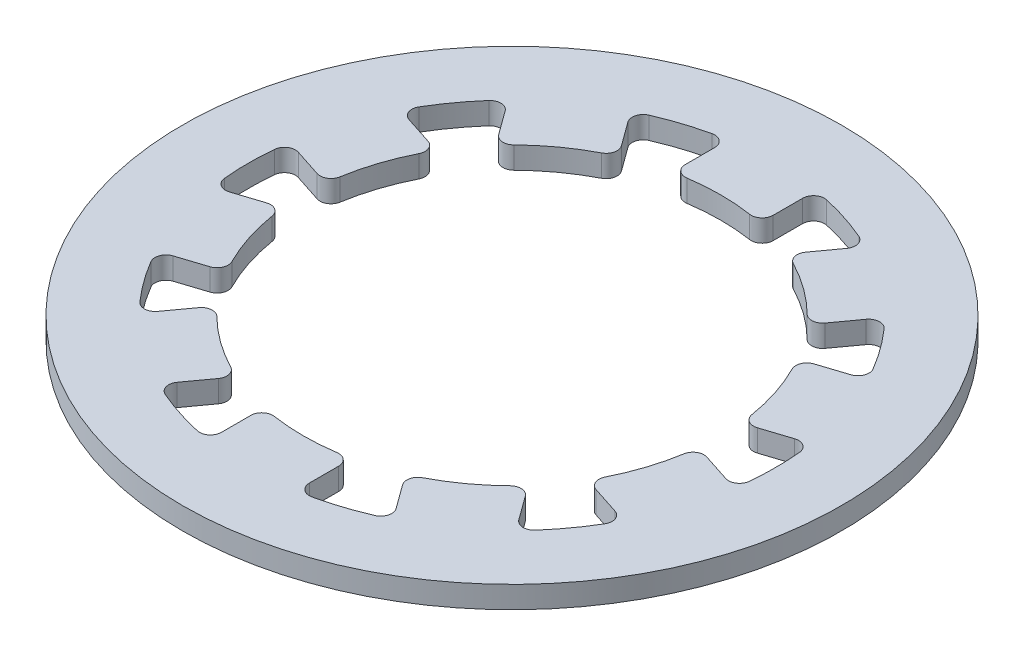
SolidWorks part; units mm, degrees
ref_plane "Front Plane" through (0, 0, 0) normal (0, 0, 1) x (1, 0, 0)
ref_plane "Top Plane" through (0, 0, 0) normal (0, 1, 0) x (1, 0, 0)
ref_plane "Right Plane" through (0, 0, 0) normal (1, 0, 0) x (0, 0, -1)
sketch "Sketch1" plane through (0, 0, 0) normal (0, 1, 0) x (1, 0, 0)
  line L0 (0, 18.9947) -> (0, -20.503) construction
  line L1 (-18.0992, 0) -> (25.0749, 0) construction
  line L2 (-2, 11.225) -> (-2, 9.8869)
  line L3 (2, 11.225) -> (2, 9.8869)
  line L4 (2, 18.9947) -> (2, -20.503) construction
  line L5 (-2, 18.9947) -> (-2, -20.503) construction
  line L6 (8.2159, 7.9056) -> (7.4294, 6.8231)
  line L7 (4.9798, 10.2568) -> (4.1933, 9.1742)
  line L8 (11.2936, 1.5666) -> (10.021, 1.1531)
  line L9 (10.0575, 5.3708) -> (8.7849, 4.9573)
  line L10 (10.0575, -5.3708) -> (8.7849, -4.9573)
  line L11 (11.2936, -1.5666) -> (10.021, -1.1531)
  line L12 (4.9798, -10.2568) -> (4.1933, -9.1742)
  line L13 (8.2159, -7.9056) -> (7.4294, -6.8231)
  line L14 (-2, -11.225) -> (-2, -9.8869)
  line L15 (2, -11.225) -> (2, -9.8869)
  line L16 (-8.2159, -7.9056) -> (-7.4294, -6.8231)
  line L17 (-4.9798, -10.2568) -> (-4.1933, -9.1742)
  line L18 (-11.2936, -1.5666) -> (-10.021, -1.1531)
  line L19 (-10.0575, -5.3708) -> (-8.7849, -4.9573)
  line L20 (-10.0575, 5.3708) -> (-8.7849, 4.9573)
  line L21 (-11.2936, 1.5666) -> (-10.021, 1.1531)
  line L22 (-4.9798, 10.2568) -> (-4.1933, 9.1742)
  line L23 (-8.2159, 7.9056) -> (-7.4294, 6.8231)
  circle A0 centre (0, 0) radius 15
  arc A1 (-4.3679, 8.4363) -> (-6.6736, 6.7611) centre (0, 0) ccw
  arc A2 (-8.9952, 7.9427) -> (-10.3336, 6.1005) centre (0, 0) ccw
  arc A3 (-8.4925, 4.2577) -> (-9.3732, 1.5472) centre (0, 0) ccw
  arc A4 (-9.3732, -1.5472) -> (-8.4925, -4.2577) centre (0, 0) ccw
  arc A5 (-6.6736, -6.7611) -> (-4.3679, -8.4363) centre (0, 0) ccw
  arc A6 (-1.425, -9.3925) -> (1.425, -9.3925) centre (0, 0) ccw
  arc A7 (4.3679, -8.4363) -> (6.6736, -6.7611) centre (0, 0) ccw
  arc A8 (8.4925, -4.2577) -> (9.3732, -1.5472) centre (0, 0) ccw
  arc A9 (9.3732, 1.5472) -> (8.4925, 4.2577) centre (0, 0) ccw
  arc A10 (6.6736, 6.7611) -> (4.3679, 8.4363) centre (0, 0) ccw
  arc A11 (1.425, 9.3925) -> (-1.425, 9.3925) centre (0, 0) ccw
  arc A12 (-11.9459, 1.1385) -> (-11.9459, -1.1385) centre (0, 0) ccw
  arc A13 (-10.3336, -6.1005) -> (-8.9952, -7.9427) centre (0, 0) ccw
  arc A14 (-4.7743, -11.0094) -> (-2.6087, -11.713) centre (0, 0) ccw
  arc A15 (2.6087, -11.713) -> (4.7743, -11.0094) centre (0, 0) ccw
  arc A16 (8.9952, -7.9427) -> (10.3336, -6.1005) centre (0, 0) ccw
  arc A17 (11.9459, -1.1385) -> (11.9459, 1.1385) centre (0, 0) ccw
  arc A18 (10.3336, 6.1005) -> (8.9952, 7.9427) centre (0, 0) ccw
  arc A19 (-2.6087, 11.713) -> (-4.7743, 11.0094) centre (0, 0) ccw
  arc A20 (4.7743, 11.0094) -> (2.6087, 11.713) centre (0, 0) ccw
  arc A21 (-11.2936, 1.5666) -> (-11.9459, 1.1385) centre (-11.4481, 1.0911) ccw
  arc A22 (-11.2936, -1.5666) -> (-11.9459, -1.1385) centre (-11.4481, -1.0911) cw
  arc A23 (-10.021, -1.1531) -> (-9.3732, -1.5472) centre (-9.8665, -1.6286) cw
  arc A24 (-8.7849, -4.9573) -> (-8.4925, -4.2577) centre (-8.9394, -4.4818) ccw
  arc A25 (-10.0575, -5.3708) -> (-10.3336, -6.1005) centre (-9.903, -5.8463) ccw
  arc A26 (-8.2159, -7.9056) -> (-8.9952, -7.9427) centre (-8.6204, -7.6117) cw
  arc A27 (-7.4294, -6.8231) -> (-6.6736, -6.7611) centre (-7.0249, -7.117) cw
  arc A28 (-4.1933, -9.1742) -> (-4.3679, -8.4363) centre (-4.5978, -8.8803) ccw
  arc A29 (-4.9798, -10.2568) -> (-4.7743, -11.0094) centre (-4.5753, -10.5507) ccw
  arc A30 (-2, -11.225) -> (-2.6087, -11.713) centre (-2.5, -11.225) cw
  arc A31 (-2, -9.8869) -> (-1.425, -9.3925) centre (-1.5, -9.8869) cw
  arc A32 (2, -9.8869) -> (1.425, -9.3925) centre (1.5, -9.8869) ccw
  arc A33 (2, -11.225) -> (2.6087, -11.713) centre (2.5, -11.225) ccw
  arc A34 (4.9798, -10.2568) -> (4.7743, -11.0094) centre (4.5753, -10.5507) cw
  arc A35 (4.1933, -9.1742) -> (4.3679, -8.4363) centre (4.5978, -8.8803) cw
  arc A36 (7.4294, -6.8231) -> (6.6736, -6.7611) centre (7.0249, -7.117) ccw
  arc A37 (8.2159, -7.9056) -> (8.9952, -7.9427) centre (8.6204, -7.6117) ccw
  arc A38 (10.0575, -5.3708) -> (10.3336, -6.1005) centre (9.903, -5.8463) cw
  arc A39 (8.7849, -4.9573) -> (8.4925, -4.2577) centre (8.9394, -4.4818) cw
  arc A40 (10.021, -1.1531) -> (9.3732, -1.5472) centre (9.8665, -1.6286) ccw
  arc A41 (11.2936, -1.5666) -> (11.9459, -1.1385) centre (11.4481, -1.0911) ccw
  arc A42 (11.2936, 1.5666) -> (11.9459, 1.1385) centre (11.4481, 1.0911) cw
  arc A43 (10.021, 1.1531) -> (9.3732, 1.5472) centre (9.8665, 1.6286) cw
  arc A44 (8.7849, 4.9573) -> (8.4925, 4.2577) centre (8.9394, 4.4818) ccw
  arc A45 (10.0575, 5.3708) -> (10.3336, 6.1005) centre (9.903, 5.8463) ccw
  arc A46 (8.2159, 7.9056) -> (8.9952, 7.9427) centre (8.6204, 7.6117) cw
  arc A47 (7.4294, 6.8231) -> (6.6736, 6.7611) centre (7.0249, 7.117) cw
  arc A48 (4.1933, 9.1742) -> (4.3679, 8.4363) centre (4.5978, 8.8803) ccw
  arc A49 (4.9798, 10.2568) -> (4.7743, 11.0094) centre (4.5753, 10.5507) ccw
  arc A50 (2, 11.225) -> (2.6087, 11.713) centre (2.5, 11.225) cw
  arc A51 (2, 9.8869) -> (1.425, 9.3925) centre (1.5, 9.8869) cw
  arc A52 (-2, 9.8869) -> (-1.425, 9.3925) centre (-1.5, 9.8869) ccw
  arc A53 (-2, 11.225) -> (-2.6087, 11.713) centre (-2.5, 11.225) ccw
  arc A54 (-7.4294, 6.8231) -> (-6.6736, 6.7611) centre (-7.0249, 7.117) ccw
  arc A55 (-4.1933, 9.1742) -> (-4.3679, 8.4363) centre (-4.5978, 8.8803) cw
  arc A56 (-4.9798, 10.2568) -> (-4.7743, 11.0094) centre (-4.5753, 10.5507) cw
  arc A57 (-10.021, 1.1531) -> (-9.3732, 1.5472) centre (-9.8665, 1.6286) ccw
  arc A58 (-8.7849, 4.9573) -> (-8.4925, 4.2577) centre (-8.9394, 4.4818) cw
  arc A59 (-8.2159, 7.9056) -> (-8.9952, 7.9427) centre (-8.6204, 7.6117) ccw
  arc A60 (-10.0575, 5.3708) -> (-10.3336, 6.1005) centre (-9.903, 5.8463) cw
  point P55 (0, 0)
  point P113 (2, 11.8322)
  point P116 (2, 9.2871)
  point P121 (-2, 11.8322)
  dimension "D1" = 30
  dimension "D2" = 19
  dimension "D5" = 24
  dimension "D7" = 0.5
  dimension "D3" = 2
  dimension "D4" = 2
  dimension "D6" = 10
extrude "Boss-Extrude1" add sketch "Sketch1" along normal blind 1
